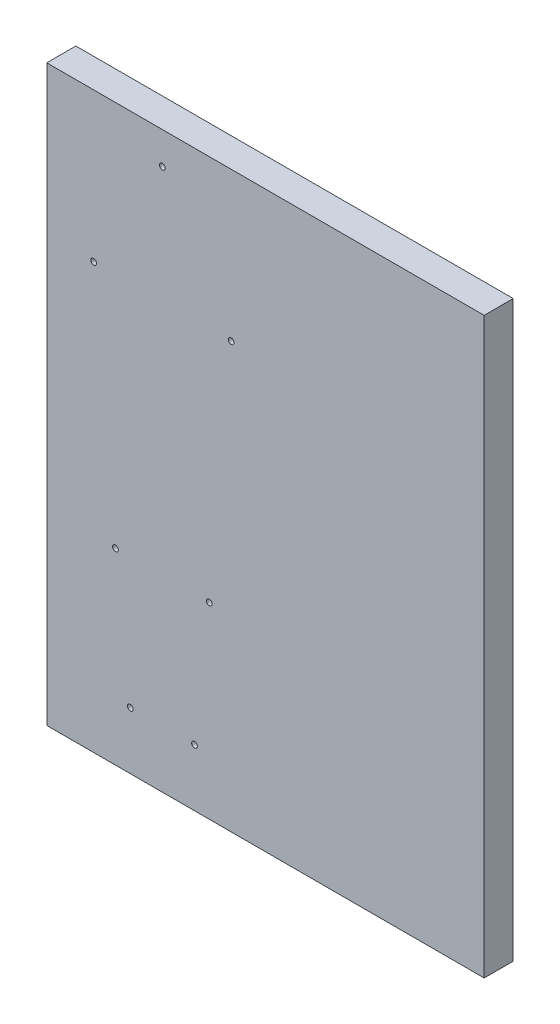
SolidWorks part; units mm, degrees
ref_plane "Front Plane" through (0, 0, 0) normal (0, 0, 1) x (1, 0, 0)
ref_plane "Top Plane" through (0, 0, 0) normal (0, 1, 0) x (1, 0, 0)
ref_plane "Right Plane" through (0, 0, 0) normal (1, 0, 0) x (0, 0, -1)
sketch "Sketch1" plane through (0, 0, 0) normal (0, 0, 1) x (1, 0, 0)
  line L0 (25, 109.8747) -> (25, -0.1253) construction
  line L1 (-25.5, 70) -> (165.5, 70)
  line L2 (-25.5, 70) -> (-25.5, -180.6)
  line L3 (-25.5, -180.6) -> (165.5, -180.6)
  line L4 (165.5, 70) -> (165.5, -180.6)
  line L5 (25, -180.6) -> (25, 70) construction
  line L7 (22, 60) -> (28, 60) construction
  line L8 (45, -170.6) -> (5, -170.6) construction
  line L10 (-15.5, 52) -> (-15.5, 12) construction
  line L11 (65.5, 52) -> (65.5, 12) construction
  point P556 (25, 0)
  dimension "D1" = 10
  dimension "D2" = 10
  dimension "D3" = 10
  dimension "D4" = 100
extrude "Boss-Extrude1" add sketch "Sketch1" along normal blind 12.7
sketch "Sketch2" plane through (0, 0, 0) normal (0, 0, -1) x (-1, 0, 0)
  line L0 (-40.7, -155.6) -> (-37.3, -155.6) construction
  line L1 (-40.7, -163.1) -> (-40.7, -148.1) construction
  line L2 (-37.3, -163.1) -> (-37.3, -148.1) construction
  line L4 (-12.7, -155.6) -> (-9.3, -155.6) construction
  line L5 (-12.7, -163.1) -> (-12.7, -148.1) construction
  line L6 (-9.3, -163.1) -> (-9.3, -148.1) construction
  point P0 (-25, 56)
  point P3 (-55, 5)
  point P6 (5, 5)
  point P9 (-45.5, -98.6)
  point P12 (-4.5, -98.6)
  point P32 (-11, -155.6)
  point P34 (-39, -155.6)
hole_wizard "M3x0.5 Tapped Hole1" positions "Sketch2" profile "Sketch3" tap size "M3x0.5" standard "ANSI Metric" end condition through all
sketch "Sketch3" plane through (25, 56, 0) normal (1, 0, 0) x (0, 1, 0)
  line L0 (0, 0) -> (0, 12.7)
  line L1 (0, 12.7) -> (1.25, 12.7)
  line L2 (1.25, 12.7) -> (1.25, 0)
  line L5 (1.25, 0) -> (0, 0)
  line L11 (0, -6.35) -> (0, 107.95) construction
  dimension "Thru Tap Drill Dia." = 2.5
  dimension "Thru Tap Drill Depth" = 12.7
cosmetic thread "Hole Thread1"
cosmetic thread "Hole Thread2"
cosmetic thread "Hole Thread3"
cosmetic thread "Hole Thread4"
cosmetic thread "Hole Thread5"
cosmetic thread "Hole Thread6"
cosmetic thread "Hole Thread7"
